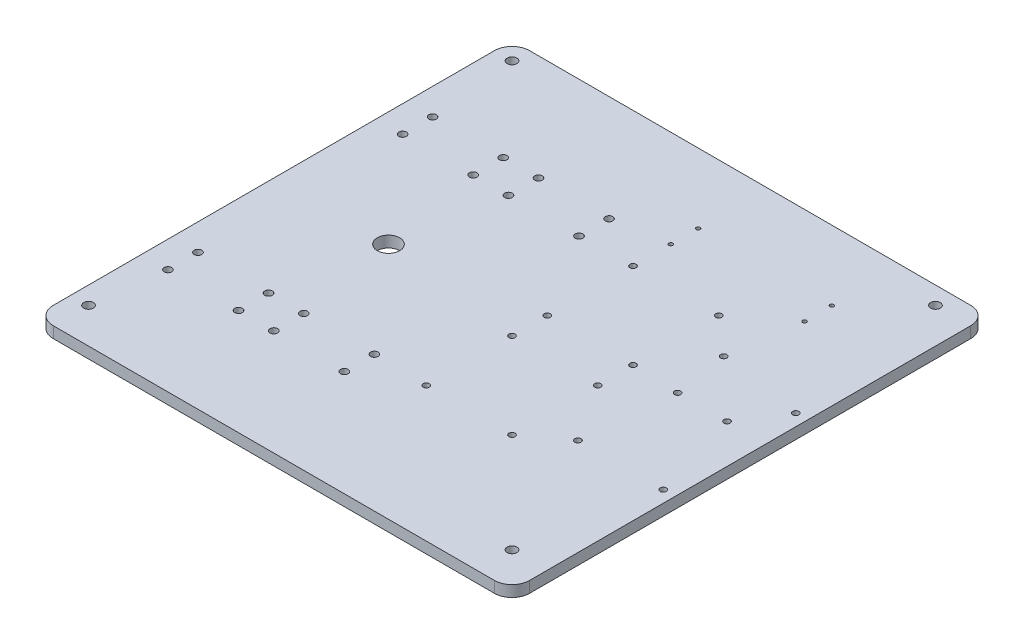
SolidWorks part; units mm, degrees
material "Acrylic (Medium-high impact)"
ref_plane "Front Plane" through (0, 0, 0) normal (0, 0, 1) x (1, 0, 0)
ref_plane "Top Plane" through (0, 0, 0) normal (0, 1, 0) x (1, 0, 0)
ref_plane "Right Plane" through (0, 0, 0) normal (1, 0, 0) x (0, 0, -1)
sketch "Sketch1" plane through (0, 0, 0) normal (0, 1, 0) x (1, 0, 0)
  line L0 (-65, 135) -> (0, 0) construction
  line L1 (-65, 135) -> (205, 135)
  line L2 (-65, 135) -> (-65, -135)
  line L3 (-65, -135) -> (205, -135)
  line L4 (205, 135) -> (205, -135)
  line L5 (0, 0) -> (-65, -135) construction
  dimension "D1" = 270
  dimension "D2" = 65
extrude "Boss-Extrude1" add sketch "Sketch1" along normal blind 6.35
sketch "Sketch3" plane through (0, 6.35, 0) normal (0, 1, 0) x (1, 0, 0)
  line L1 (-50, -58) -> (-10, -58) construction
  line L2 (-50, -58) -> (-50, -75) construction
  line L3 (-50, -75) -> (-10, -75) construction
  line L4 (-10, -58) -> (-10, -75) construction
  circle A0 centre (-50, -58) radius 2.15
  circle A1 centre (-10, -58) radius 2.15
  circle A2 centre (-50, -75) radius 2.15
  circle A3 centre (-10, -75) radius 2.15
  dimension "D3" = 4.3
  dimension "D1" = 40
  dimension "D2" = 17
  dimension "D4" = 10
  dimension "D5" = 58
extrude "Cut-Extrude1" cut sketch "Sketch3" against normal through all
mirror "Mirror1" about plane through (0, 0, 0) normal (1, 0, 0) of "Cut-Extrude1"
mirror "Mirror2" about plane through (0, 0, 0) normal (0, 0, 1) of "Mirror1", "Cut-Extrude1"
sketch "Sketch4" plane through (0, 6.35, 0) normal (0, 1, 0) x (1, 0, 0)
  circle A0 centre (0, 0) radius 6.35
  dimension "D1" = 12.7
extrude "Cut-Extrude2" cut sketch "Sketch4" against normal through all
sketch "Sketch6" plane through (0, 0, 0) normal (0, -1, 0) x (1, 0, 0)
  line L1 (80, -58.6) -> (128.6, -58.6) construction
  line L2 (80, -58.6) -> (80, -10) construction
  line L3 (80, -10) -> (128.6, -10) construction
  line L4 (128.6, -58.6) -> (128.6, -10) construction
  line L5 (80, 10) -> (128.6, 10) construction
  line L6 (80, 10) -> (80, 58.6) construction
  line L7 (80, 58.6) -> (128.6, 58.6) construction
  line L8 (128.6, 10) -> (128.6, 58.6) construction
  circle A0 centre (80, -58.6) radius 1.75
  circle A1 centre (80, -10) radius 1.75
  circle A2 centre (128.6, -58.6) radius 1.75
  circle A3 centre (128.6, -10) radius 1.75
  circle A4 centre (80, 10) radius 1.75
  circle A5 centre (80, 58.6) radius 1.75
  circle A6 centre (128.6, 58.6) radius 1.75
  circle A7 centre (128.6, 10) radius 1.75
  circle A8 centre (198.3362, 42.6262) radius 1.75
  circle A9 centre (150, 42.6262) radius 1.75
  circle A10 centre (150, -40) radius 1.75
  circle A11 centre (154.8785, -8.9993) radius 1.75
  circle A12 centre (198.3362, -32.507) radius 1.75
  circle A13 centre (182.8947, -8.9993) radius 1.75
  dimension "D1" = 3.5
  dimension "D2" = 48.6
  dimension "D3" = 3.5
  dimension "D4" = 48.3362
  dimension "D5" = 51.6255
  dimension "D6" = 15.4415
  dimension "D7" = 75.1332
  dimension "D8" = 82.6262
  dimension "D9" = 43.4577
  dimension "D10" = 48.3362
  dimension "D14" = 150
  dimension "D11" = 10
  dimension "D12" = 10
  dimension "D13" = 80
  dimension "D15" = 40
extrude "Cut-Extrude4" cut sketch "Sketch6" against normal through all
sketch "Sketch7" plane through (0, 0, 0) normal (0, -1, 0) x (1, 0, 0)
  line L0 (155.8, -95.5) -> (155.8, -80) construction
  line L1 (155.8, -95.5) -> (80, -95.5) construction
  line L2 (155.8, -80) -> (80, -80) construction
  line L3 (80, -95.5) -> (80, -80) construction
  line L4 (80, -58.6) -> (80, -80) construction
  circle A0 centre (155.8, -95.5) radius 1.1
  circle A1 centre (80, -95.5) radius 1.1
  circle A2 centre (80, -80) radius 1.1
  circle A3 centre (155.8, -80) radius 1.1
  dimension "D3" = 2.2
  dimension "D1" = 15.5
  dimension "D2" = 75.8
  dimension "D4" = 80
extrude "Cut-Extrude5" cut sketch "Sketch7" against normal through all
fillet "Fillet1" radius 10 4 edges at (205, 3.175, 135) (205, 3.175, -135) (-65, 3.175, 135) (-65, 3.175, -135)
sketch "Sketch8" plane through (0, 6.35, 0) normal (0, 1, 0) x (1, 0, 0)
  line L0 (-55, 125) -> (185, 125) construction
  line L1 (185, 125) -> (185, -115) construction
  line L2 (185, -115) -> (-55, -115) construction
  line L3 (-55, 125) -> (-55, -115) construction
  line L4 (205, -125) -> (205, 125) construction
  line L5 (195, 135) -> (-55, 135) construction
  line L6 (-65, 125) -> (-65, -125) construction
  circle A0 centre (-55, 125) radius 2.75
  circle A1 centre (185, 125) radius 2.75
  circle A2 centre (-55, -115) radius 2.75
  circle A3 centre (185, -115) radius 2.75
  dimension "D1" = 5.5
  dimension "D2" = 20
  dimension "D3" = 10
  dimension "D4" = 10
extrude "Cut-Extrude6" cut sketch "Sketch8" against normal up to next
